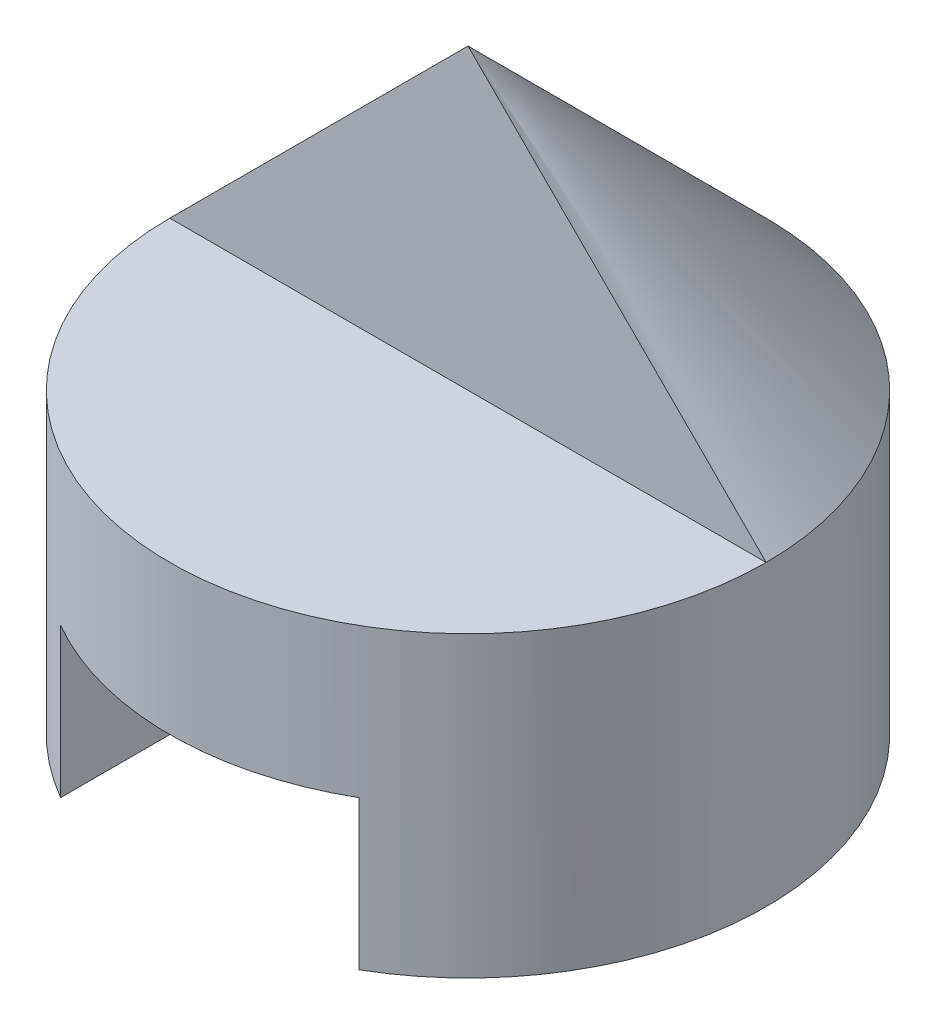
SolidWorks part; units mm, degrees
ref_plane "Front Plane" through (0, 0, 0) normal (0, 0, 1) x (1, 0, 0)
ref_plane "Top Plane" through (0, 0, 0) normal (0, 1, 0) x (1, 0, 0)
ref_plane "Right Plane" through (0, 0, 0) normal (1, 0, 0) x (0, 0, -1)
sketch "Sketch1" plane through (0, 0, 0) normal (0, 0, 1) x (1, 0, 0)
  line L1 (0, 0) -> (40, 0)
  line L2 (0, 0) -> (0, 40)
  line L3 (0, 40) -> (40, 40)
  line L4 (40, 0) -> (40, 40)
  dimension "D1" = 40
  dimension "D2" = 40
extrude "Boss-Extrude1" add sketch "Sketch1" along normal blind 40
sketch "Sketch2" plane through (0, 0, 40) normal (0, 0, 1) x (1, 0, 0)
  line L0 (0, 20) -> (20, 40)
  line L1 (0, 40) -> (0, 0) construction
  line L2 (40, 40) -> (0, 40) construction
  line L3 (20, 40) -> (0, 40)
  line L4 (0, 40) -> (0, 20)
  line L5 (20, 40) -> (40, 20)
  line L6 (40, 0) -> (40, 40) construction
  line L7 (40, 20) -> (40, 40)
  line L8 (40, 40) -> (20, 40)
  line L9 (10, 0) -> (10, 10)
  line L10 (0, 0) -> (40, 0) construction
  line L11 (10, 10) -> (30, 10)
  line L12 (30, 10) -> (30, 0)
  line L13 (30, 0) -> (10, 0)
  line M1 (0, 40) -> (0, 0)
  line M2 (0, 0) -> (40, 0)
  line M4 (40, 40) -> (0, 40)
  dimension "D1" = 20
  dimension "D2" = 10
  dimension "D3" = 10
extrude "Cut-Extrude1" cut sketch "Sketch2" against normal blind 40 contours L12 L11 L9 M2 | L0 M1 M4 | L5 L7 L8
sketch "Sketch3" plane through (0, 0, 0) normal (0, 1, 0) x (1, 0, 0)
  line L0 (20, 0) -> (20, -40) construction
  line L2 (0, 0) -> (40, 0)
  line L3 (0, 0) -> (0, -40)
  line L4 (0, -40) -> (40, -40)
  line L5 (40, 0) -> (40, -40)
  circle A0 centre (20, -20) radius 20
  dimension "D1" = 40
extrude "Cut-Extrude2" cut sketch "Sketch3" along normal blind 40 contours A0 L2 L3 | A0 L5 L2 | A0 L4 L5 | A0 L3 L4
sketch "Sketch4" plane through (0, 0, 0) normal (1, 0, 0) x (0, 0, -1)
  line L0 (-20, 20) -> (0, 20)
  line L1 (-40, 40) -> (-20, 40)
  line L2 (-40, 40) -> (-40, 20)
  line L3 (-40, 20) -> (-20, 20)
  line L4 (-20, 40) -> (-20, 20)
  line L5 (0, 10) -> (0, 40) construction
  line L6 (0, 20) -> (-20, 40)
  line L7 (-20, 40) -> (0, 40)
  line L8 (0, 40) -> (0, 20)
  dimension "D1" = 20
  dimension "D2" = 20
extrude "Cut-Extrude5" cut sketch "Sketch4" along normal blind 40 contours L8 L7 L6 | L4 L1 L2 L3
sketch "Sketch5" plane through (0, 20, 0) normal (0, 1, 0) x (1, 0, 0)
  circle A0 centre (20, -20) radius 20
extrude "Cut-Extrude6" cut sketch "Sketch5" along normal blind 30
ref_plane "Plane1" through (0, 0, 20) normal (0, 0, 1) x (1, 0, 0)
sketch "Sketch6" plane through (0, 0, 20) normal (0, 0, 1) x (1, 0, 0)
  line L0 (20, 20) -> (20, 40)
  line L1 (40, 20) -> (0, 20) construction
  line L2 (20, 40) -> (0, 20)
  line L3 (0, 20) -> (20, 20)
  dimension "D1" = 20
revolve "Revolve1" add sketch "Sketch6" angle 180 about L0
